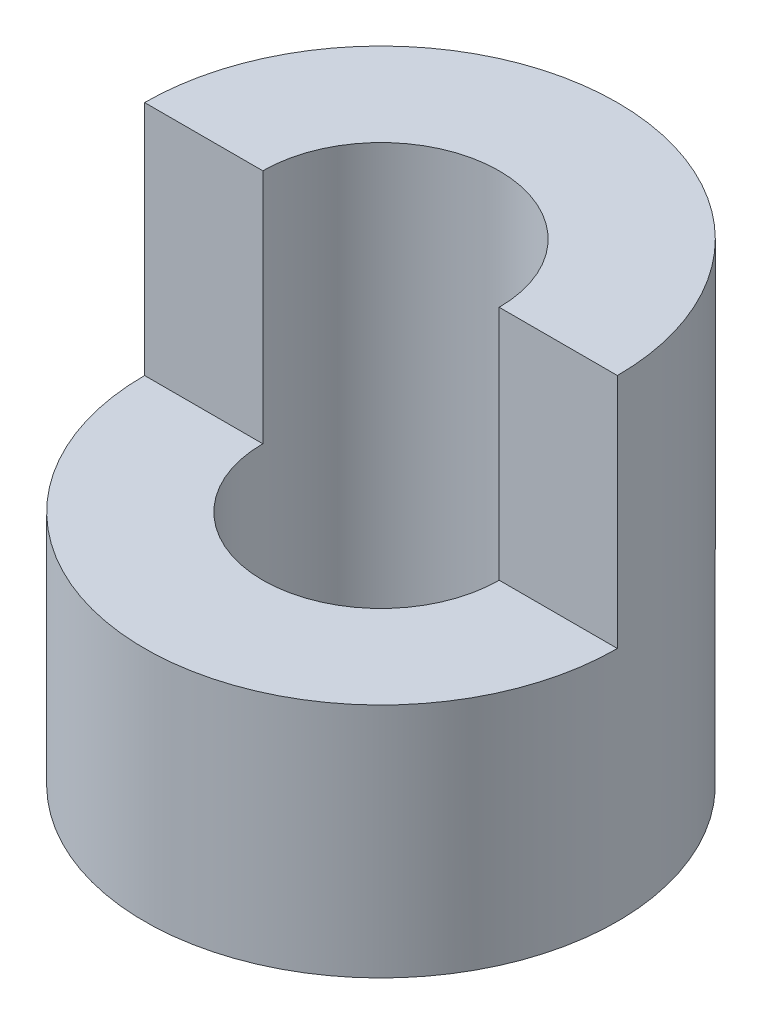
SolidWorks part; units mm, degrees
ref_plane "Front Plane" through (0, 0, 0) normal (0, 0, 1) x (1, 0, 0)
ref_plane "Top Plane" through (0, 0, 0) normal (0, 1, 0) x (1, 0, 0)
ref_plane "Right Plane" through (0, 0, 0) normal (1, 0, 0) x (0, 0, -1)
sketch "Sketch1" plane through (0, 0, 0) normal (0, 0, 1) x (1, 0, 0)
  line L1 (0, 0) -> (10, 0)
  line L2 (0, 0) -> (0, 20)
  line L3 (0, 20) -> (10, 20)
  line L4 (10, 0) -> (10, 20)
  dimension "D1" = 20
  dimension "D2" = 10
revolve "Revolve1" add sketch "Sketch1" angle 360 about L2
sketch "Sketch2" plane through (0, 20, 0) normal (0, 1, 0) x (1, 0, 0)
  circle A0 centre (0, 0) radius 5
  dimension "D1" = 10
extrude "Cut-Extrude1" cut sketch "Sketch2" against normal blind 20
sketch "Sketch3" plane through (0, 20, 0) normal (0, 1, 0) x (1, 0, 0)
  line L0 (-10, 0) -> (-5, 0)
  line L1 (5, 0) -> (10, 0)
  arc A0 (-10, 0) -> (10, 0) centre (0, 0) ccw
  circle A1 centre (0, 0) radius 10 construction
  arc A2 (-5, 0) -> (5, 0) centre (0, 0) ccw
  circle A3 centre (0, 0) radius 5 construction
  dimension "D3" = 5
  dimension "D4" = 10
  dimension "D1" = 5
  dimension "D2" = 5
extrude "Cut-Extrude2" cut sketch "Sketch3" against normal blind 10
